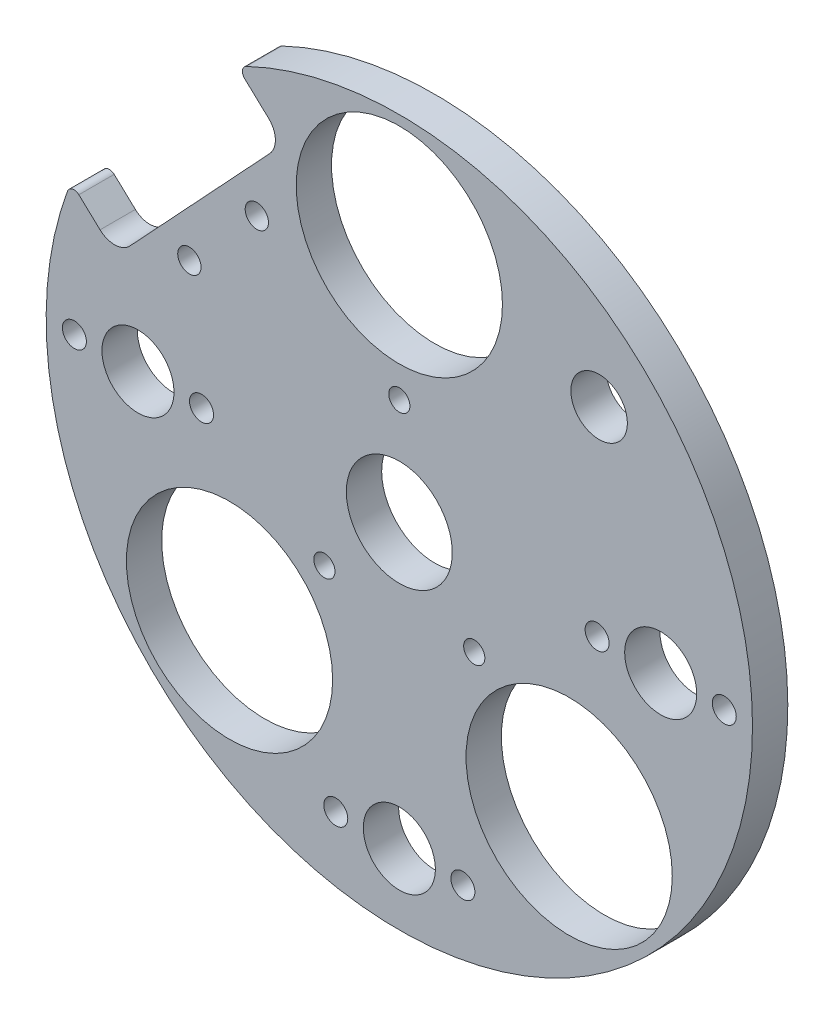
SolidWorks part; units mm, degrees
material "Acrylic (Medium-high impact)"
ref_plane "Front Plane" through (0, 0, 0) normal (0, 0, 1) x (1, 0, 0)
ref_plane "Top Plane" through (0, 0, 0) normal (0, 1, 0) x (1, 0, 0)
ref_plane "Right Plane" through (0, 0, 0) normal (1, 0, 0) x (0, 0, -1)
sketch "Sketch1" plane through (0, 0, 0) normal (0, 0, 1) x (1, 0, 0)
  circle A0 centre (0, 0) radius 50
  dimension "D1" = 100
extrude "Boss-Extrude1" add sketch "Sketch1" along normal blind 5
hole_wizard "Ø15.0 (15) Diameter Hole1" positions "Sketch3" profile "Sketch4" hole size "Ø15.0" standard "ISO" end condition through all
sketch "Sketch3" plane through (0, 0, 0) normal (0, 0, -1) x (-1, 0, 0)
  point P0 (0, 0)
sketch "Sketch4" plane through (0, 0, 0) normal (1, 0, 0) x (0, 1, 0)
  line L0 (0, 0) -> (0, 5)
  line L1 (0, 5) -> (7.5, 5)
  line L2 (7.5, 5) -> (7.5, 0)
  line L5 (7.5, 0) -> (0, 0)
  line L11 (0, -6.35) -> (0, 107.95) construction
  dimension "Thru Hole Dia." = 15
  dimension "Thru Hole Depth" = 5
hole_wizard "Ø10.2 (10.2) Diameter Hole1" positions "Sketch5" profile "Sketch6" hole size "Ø10.2" standard "ISO"
sketch "Sketch5" plane through (0, 0, 0) normal (0, 0, -1) x (-1, 0, 0)
  point P4 (37, 0)
  point P17 (-37, 0)
  point P18 (0, 0)
  point P21 (0, -37)
  point P23 (0, -40)
  dimension "D1" = 3
  dimension "D2" = 40
  dimension "D3" = 37
sketch "Sketch6" plane through (-37, 0, 0) normal (1, 0, 0) x (0, 1, 0)
  line L0 (0, 0) -> (0, 5)
  line L1 (0, 5) -> (5.1, 5)
  line L2 (5.1, 5) -> (5.1, 0)
  line L5 (5.1, 0) -> (0, 0)
  line L11 (0, -6.35) -> (0, 107.95) construction
  dimension "Thru Hole Dia." = 10.2
  dimension "Thru Hole Depth" = 5
hole_wizard "M3 Clearance Hole1" positions "Sketch7" profile "Sketch8" hole size "M3" standard "ISO" end condition through all
sketch "Sketch7" plane through (0, 0, 5) normal (0, 0, 1) x (1, 0, 0)
  circle A0 centre (37, 0) radius 5.1 construction
  circle A1 centre (0, -40) radius 5.1 construction
  point P0 (46, 0)
  point P2 (28, 0)
  point P11 (9, -40)
  point P13 (-9, -40)
  point P46 (-46, 0)
  point P47 (-28, 0)
  dimension "D2" = 9
  dimension "D1" = 9
  dimension "D4" = 9
  dimension "D5" = 9
  dimension "D6" = 2
  dimension "D3" = 40
sketch "Sketch8" plane through (46, 0, 5) normal (1, 0, 0) x (0, -1, 0)
  line L0 (0, 0) -> (0, 5)
  line L1 (0, 5) -> (1.7, 5)
  line L2 (1.7, 5) -> (1.7, 0)
  line L5 (1.7, 0) -> (0, 0)
  line L11 (0, -6.35) -> (0, 107.95) construction
  dimension "Thru Hole Dia." = 3.4
  dimension "Thru Hole Depth" = 5
sketch "Sketch9" plane through (0, 0, 5) normal (0, 0, 1) x (1, 0, 0)
  line L0 (0, 0) -> (24.0416, -24.0416) construction
  line L1 (0, 0) -> (71.3708, 0) construction
  circle A0 centre (24.0416, -24.0416) radius 14.6
  circle A1 centre (10.6066, -10.6066) radius 1.5
  circle A2 centre (-24.0416, -24.0416) radius 14.6
  circle A3 centre (-10.6066, -10.6066) radius 1.5
  circle A4 centre (0, 34) radius 14.6
  circle A5 centre (0, 15) radius 1.5
  point P13 (0, 0)
  dimension "D1" = 29.2
  dimension "D3" = 45
  dimension "D4" = 3
  dimension "D5" = 19
  dimension "D7" = 29.2
  dimension "D9" = 3
  dimension "D10" = 19
  dimension "D2" = 34
  dimension "D8" = 34
  dimension "D6" = 2
extrude "Cut-Extrude1" cut sketch "Sketch9" against normal blind 10
sketch "Sketch10" plane through (0, 0, 5) normal (0, 0, 1) x (1, 0, 0)
  line L0 (-27.2748, 48.4556) -> (-18.4986, 40.2716)
  line L1 (-18.3505, 36.0316) -> (-38.1285, 14.8223)
  line L2 (-42.3685, 14.6743) -> (-51.1448, 22.8582)
  line L3 (-51.1448, 22.8582) -> (-27.2748, 48.4556)
  line L4 (-40.1745, 12.6283) -> (-7.5635, 12.6283) construction
  line L5 (0, 0) -> (-28.2395, 25.427) construction
  circle A0 centre (-20.1744, 27.4774) radius 1.65
  circle A1 centre (-29.7224, 17.2385) radius 1.65
  arc A2 (-18.4986, 40.2716) -> (-18.3505, 36.0316) centre (-20.5446, 38.0776) cw
  arc A3 (-42.3685, 14.6743) -> (-38.1285, 14.8223) centre (-40.3225, 16.8683) ccw
  point P14 (-16.3045, 38.2257)
  dimension "D6" = 3.3
  dimension "D7" = 3.3
  dimension "D12" = 3
  dimension "D1" = 35
  dimension "D2" = 15
  dimension "D3" = 47
  dimension "D4" = 38
  dimension "D5" = 138
  dimension "D8" = 4.5
  dimension "D9" = 10.5
  dimension "D10" = 4.5
  dimension "D11" = 10.5
extrude "Cut-Extrude2" cut sketch "Sketch10" against normal blind 5 contours L3 L0 A2 L1 A3 L2 | A0 | A1
sketch "Sketch11" plane through (0, 0, 5) normal (0, 0, 1) x (1, 0, 0)
  line L0 (0, 0) -> (28.2843, 28.2843) construction
  line L1 (0, 0) -> (23.1067, 0) construction
  circle A0 centre (28.2843, 28.2843) radius 4
  dimension "D1" = 8
  dimension "D2" = 45
  dimension "D3" = 40
extrude "Cut-Extrude3" cut sketch "Sketch11" against normal blind 10
fillet "Fillet1" radius 1 2 edges at (-46.4569, 18.4867, 2.5) (-22.9494, 44.4221, 2.5)
